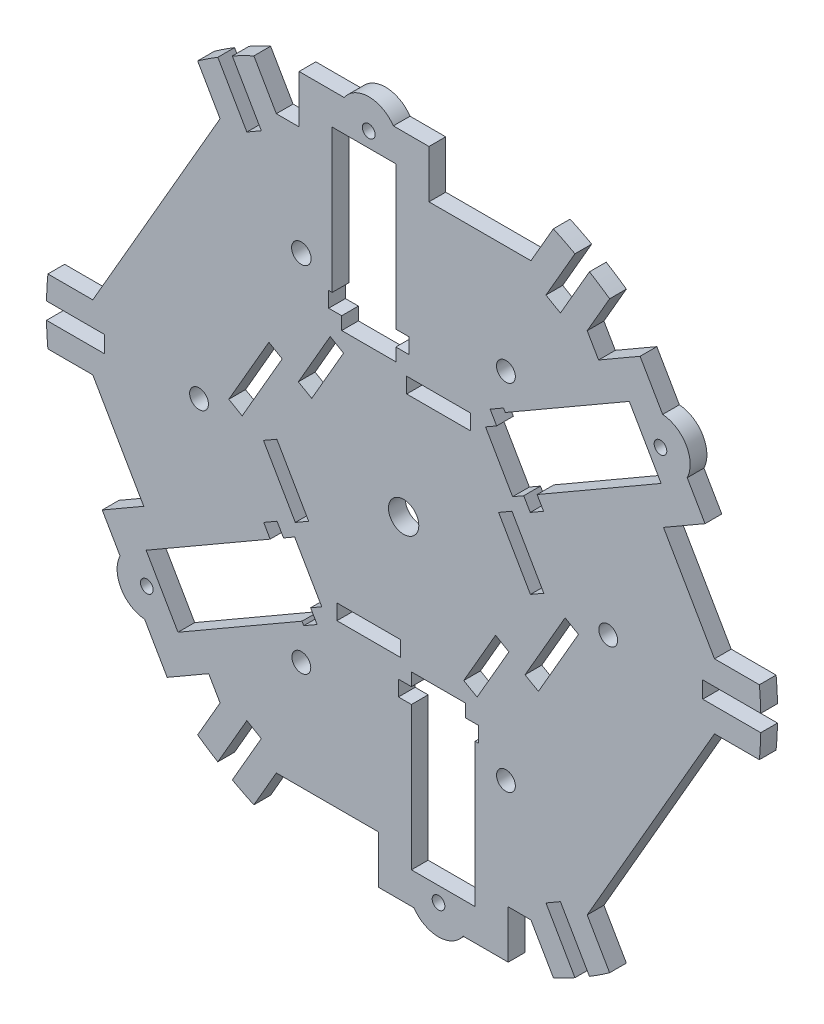
SolidWorks part; units mm, degrees
ref_plane "Front Plane" through (0, 0, 0) normal (0, 0, 1) x (1, 0, 0)
ref_plane "Top Plane" through (0, 0, 0) normal (0, 1, 0) x (1, 0, 0)
ref_plane "Right Plane" through (0, 0, 0) normal (1, 0, 0) x (0, 0, -1)
sketch "Model" plane through (0, 0, 0) normal (0, 0, 1) x (1, 0, 0)
  line L0 (33.3939, 18.31) -> (29.1071, 15.835) construction
  line L1 (43.2939, 1.1627) -> (33.3939, 18.31) construction
  line L2 (39.0071, -1.3123) -> (43.2939, 1.1627) construction
  line L3 (29.1071, 15.835) -> (39.0071, -1.3123) construction
  line L4 (32.5539, -19.765) -> (28.2671, -17.29) construction
  line L5 (22.6539, -36.9123) -> (32.5539, -19.765) construction
  line L6 (18.3671, -34.4373) -> (22.6539, -36.9123) construction
  line L7 (28.2671, -17.29) -> (18.3671, -34.4373) construction
  line L8 (-0.84, -38.075) -> (-0.84, -33.125) construction
  line L9 (-20.64, -38.075) -> (-0.84, -38.075) construction
  line L10 (-20.64, -33.125) -> (-20.64, -38.075) construction
  line L11 (-0.84, -33.125) -> (-20.64, -33.125) construction
  line L12 (-33.3939, -18.31) -> (-29.1071, -15.835) construction
  line L13 (-43.2939, -1.1627) -> (-33.3939, -18.31) construction
  line L14 (-39.0071, 1.3123) -> (-43.2939, -1.1627) construction
  line L15 (-29.1071, -15.835) -> (-39.0071, 1.3123) construction
  line L16 (-32.5539, 19.765) -> (-28.2671, 17.29) construction
  line L17 (-22.6539, 36.9123) -> (-32.5539, 19.765) construction
  line L18 (-18.3671, 34.4373) -> (-22.6539, 36.9123) construction
  line L19 (-28.2671, 17.29) -> (-18.3671, 34.4373) construction
  line L20 (36.9463, 23.9861) -> (38.946, 20.5225) construction
  line L21 (33.5255, 22.0111) -> (36.9463, 23.9861) construction
  line L22 (25.0855, 36.6296) -> (33.5255, 22.0111) construction
  line L23 (28.5063, 38.6046) -> (25.0855, 36.6296) construction
  line L24 (26.506, 42.0692) -> (28.5063, 38.6046) construction
  line L25 (30.7928, 44.5442) -> (26.506, 42.0692) construction
  line L26 (30.7928, 44.5442) -> (31.3331, 43.6084) construction
  line L27 (33.3573, 18.1734) -> (29.2437, 15.7984)
  line L28 (69.5248, 65.6584) -> (31.3331, 43.6084) construction
  line L29 (79.4248, 48.5111) -> (69.5248, 65.6584) construction
  line L30 (41.2331, 26.4611) -> (79.4248, 48.5111) construction
  line L31 (43.2328, 22.9975) -> (41.2331, 26.4611) construction
  line L32 (38.946, 20.5225) -> (43.2328, 22.9975) construction
  line L33 (37.246, -23.467) -> (41.5328, -25.942) construction
  line L34 (49.686, -1.9203) -> (37.246, -23.467) construction
  line L35 (53.9728, -4.3953) -> (49.686, -1.9203) construction
  line L36 (41.5328, -25.942) -> (53.9728, -4.3953) construction
  line L37 (2.3, -43.9895) -> (-1.7, -43.9895) construction
  line L38 (2.3, -40.0395) -> (2.3, -43.9895) construction
  line L39 (19.18, -40.0395) -> (2.3, -40.0395) construction
  line L40 (19.18, -43.9895) -> (19.18, -40.0395) construction
  line L41 (23.18, -43.9895) -> (19.18, -43.9895) construction
  line L42 (23.18, -48.9395) -> (23.18, -43.9895) construction
  line L43 (22.1, -48.9395) -> (23.18, -48.9395) construction
  line L44 (22.1, -93.0395) -> (22.1, -48.9395) construction
  line L45 (2.3, -93.0395) -> (22.1, -93.0395) construction
  line L46 (2.3, -48.9395) -> (2.3, -93.0395) construction
  line L47 (-1.7, -48.9395) -> (2.3, -48.9395) construction
  line L48 (-1.7, -43.9895) -> (-1.7, -48.9395) construction
  line L49 (-36.9457, -23.9871) -> (-38.946, -20.5225) construction
  line L50 (-33.5249, -22.0121) -> (-36.9457, -23.9871) construction
  line L51 (-25.0849, -36.6306) -> (-33.5249, -22.0121) construction
  line L52 (-28.5057, -38.6056) -> (-25.0849, -36.6306) construction
  line L53 (-26.506, -42.0692) -> (-28.5057, -38.6056) construction
  line L54 (-30.7928, -44.5442) -> (-26.506, -42.0692) construction
  line L55 (-31.3325, -43.6094) -> (-30.7928, -44.5442) construction
  line L56 (-69.5242, -65.6594) -> (-31.3325, -43.6094) construction
  line L57 (-79.4242, -48.5121) -> (-69.5242, -65.6594) construction
  line L58 (-41.2325, -26.4621) -> (-79.4242, -48.5121) construction
  line L59 (-43.2328, -22.9975) -> (-41.2325, -26.4621) construction
  line L60 (-38.946, -20.5225) -> (-43.2328, -22.9975) construction
  line L61 (-37.246, 23.467) -> (-41.5328, 25.942) construction
  line L62 (-49.686, 1.9203) -> (-37.246, 23.467) construction
  line L63 (-53.9728, 4.3953) -> (-49.686, 1.9203) construction
  line L64 (-41.5328, 25.942) -> (-53.9728, 4.3953) construction
  line L65 (0.84, 38.075) -> (0.84, 33.125) construction
  line L66 (20.64, 38.075) -> (0.84, 38.075) construction
  line L67 (20.64, 33.125) -> (20.64, 38.075) construction
  line L68 (0.84, 33.125) -> (20.64, 33.125) construction
  line L69 (-2.3, 43.9895) -> (1.7, 43.9895) construction
  line L70 (-2.3, 40.0395) -> (-2.3, 43.9895) construction
  line L71 (-19.18, 40.0395) -> (-2.3, 40.0395) construction
  line L72 (-19.18, 43.9895) -> (-19.18, 40.0395) construction
  line L73 (-23.18, 43.9895) -> (-19.18, 43.9895) construction
  line L74 (-23.18, 48.9395) -> (-23.18, 43.9895) construction
  line L75 (-22.1, 48.9395) -> (-23.18, 48.9395) construction
  line L76 (-22.1, 93.0395) -> (-22.1, 48.9395) construction
  line L77 (-2.3, 93.0395) -> (-22.1, 93.0395) construction
  line L78 (-2.3, 48.9395) -> (-2.3, 93.0395) construction
  line L79 (1.7, 48.9395) -> (-2.3, 48.9395) construction
  line L80 (1.7, 43.9895) -> (1.7, 48.9395) construction
  line L81 (43.9566, 81.085) -> (48.2434, 78.61) construction
  line L82 (52.8927, 96.5628) -> (43.9566, 81.085) construction
  line L83 (46.071, 99.9974) -> (39.1423, 87.9964) construction
  line L84 (39.1423, 87.9964) -> (7.9, 87.9964) construction
  line L85 (7.9, 87.9964) -> (7.9, 102.7645) construction
  line L86 (7.9, 102.7645) -> (-3.1242, 102.7645) construction
  line L87 (-18.3558, 102.7645) -> (-32.3, 102.7645) construction
  line L88 (-32.3, 102.7645) -> (-32.3, 87.9964) construction
  line L89 (-32.3, 87.9964) -> (-39.1423, 87.9964) construction
  line L90 (-39.1423, 87.9964) -> (-46.071, 99.9974) construction
  line L91 (-43.9566, 81.085) -> (-52.8927, 96.5628) construction
  line L92 (-48.2434, 78.61) -> (-43.9566, 81.085) construction
  line L93 (-57.1795, 94.0878) -> (-48.2434, 78.61) construction
  line L94 (-63.565, 89.8972) -> (-56.6362, 77.8962) construction
  line L95 (-56.6362, 77.8962) -> (-95.7785, 10.0998) construction
  line L96 (-95.7785, 10.0998) -> (-109.6358, 10.0998) construction
  line L97 (-92.2, 2.475) -> (-110.0722, 2.475) construction
  line L98 (-92.2, -2.475) -> (-92.2, 2.475) construction
  line L99 (-110.0722, -2.475) -> (-92.2, -2.475) construction
  line L100 (-109.6357, -10.1005) -> (-95.7779, -10.1005) construction
  line L101 (-95.7779, -10.1005) -> (-80.1568, -37.1571) construction
  line L102 (-80.1568, -37.1571) -> (-92.9463, -44.5411) construction
  line L103 (-92.9463, -44.5411) -> (-87.4342, -54.0884) construction
  line L104 (-79.8184, -67.2793) -> (-72.8463, -79.3553) construction
  line L105 (-72.8463, -79.3553) -> (-60.0568, -71.9713) construction
  line L106 (-60.0568, -71.9713) -> (-56.6357, -77.8969) construction
  line L107 (-56.6357, -77.8969) -> (-63.5643, -89.8976) construction
  line L108 (-48.2434, -78.61) -> (-57.1795, -94.0878) construction
  line L109 (-43.9566, -81.085) -> (-48.2434, -78.61) construction
  line L110 (-52.8927, -96.5628) -> (-43.9566, -81.085) construction
  line L111 (-46.071, -99.9974) -> (-39.1423, -87.9964) construction
  line L112 (-39.1423, -87.9964) -> (-7.9, -87.9964) construction
  line L113 (-7.9, -87.9964) -> (-7.9, -102.7645) construction
  line L114 (-7.9, -102.7645) -> (3.1242, -102.7645) construction
  line L115 (18.3558, -102.7645) -> (32.3, -102.7645) construction
  line L116 (32.3, -102.7645) -> (32.3, -87.9964) construction
  line L117 (32.3, -87.9964) -> (39.1423, -87.9964) construction
  line L118 (39.1423, -87.9964) -> (46.071, -99.9974) construction
  line L119 (43.9566, -81.085) -> (52.8927, -96.5628) construction
  line L120 (48.2434, -78.61) -> (43.9566, -81.085) construction
  line L121 (57.1795, -94.0878) -> (48.2434, -78.61) construction
  line L122 (63.5645, -89.8975) -> (56.6358, -77.8966) construction
  line L123 (56.6358, -77.8966) -> (95.778, -10.1002) construction
  line L124 (95.778, -10.1002) -> (109.6357, -10.1002) construction
  line L125 (92.2, -2.475) -> (110.0722, -2.475) construction
  line L126 (92.2, 2.475) -> (92.2, -2.475) construction
  line L127 (110.0722, 2.475) -> (92.2, 2.475) construction
  line L128 (109.6358, 10.0995) -> (95.7786, 10.0995) construction
  line L129 (95.7786, 10.0995) -> (80.1574, 37.1561) construction
  line L130 (80.1574, 37.1561) -> (92.9469, 44.5402) construction
  line L131 (92.9469, 44.5402) -> (87.4348, 54.0874) construction
  line L132 (79.8191, 67.2783) -> (72.8469, 79.3544) construction
  line L133 (72.8469, 79.3544) -> (60.0574, 71.9703) construction
  line L134 (60.0574, 71.9703) -> (56.6363, 77.8959) construction
  line L135 (56.6363, 77.8959) -> (63.5652, 89.8971) construction
  line L136 (48.2434, 78.61) -> (57.1795, 94.0878) construction
  line L137 (29.2437, 15.7984) -> (39.0437, -1.1757)
  line L138 (39.0437, -1.1757) -> (43.1573, 1.1993)
  line L139 (43.1573, 1.1993) -> (33.3573, 18.1734)
  line L140 (32.4173, -19.8016) -> (28.3037, -17.4266)
  line L141 (28.3037, -17.4266) -> (18.5037, -34.4007)
  line L142 (18.5037, -34.4007) -> (22.6173, -36.7757)
  line L143 (22.6173, -36.7757) -> (32.4173, -19.8016)
  line L144 (-0.94, -37.975) -> (-0.94, -33.225)
  line L145 (-0.94, -33.225) -> (-20.54, -33.225)
  line L146 (-20.54, -33.225) -> (-20.54, -37.975)
  line L147 (-20.54, -37.975) -> (-0.94, -37.975)
  line L148 (-33.3573, -18.1734) -> (-29.2437, -15.7984)
  line L149 (-29.2437, -15.7984) -> (-39.0437, 1.1757)
  line L150 (-39.0437, 1.1757) -> (-43.1573, -1.1993)
  line L151 (-43.1573, -1.1993) -> (-33.3573, -18.1734)
  line L152 (-32.4173, 19.8016) -> (-28.3037, 17.4266)
  line L153 (-28.3037, 17.4266) -> (-18.5037, 34.4007)
  line L154 (-18.5037, 34.4007) -> (-22.6173, 36.7757)
  line L155 (-22.6173, 36.7757) -> (-32.4173, 19.8016)
  line L156 (36.9829, 24.1227) -> (38.9826, 20.6591)
  line L157 (38.9826, 20.6591) -> (43.0962, 23.0341)
  line L158 (43.0962, 23.0341) -> (41.0965, 26.4977)
  line L159 (41.0965, 26.4977) -> (79.2882, 48.5477)
  line L160 (79.2882, 48.5477) -> (69.4882, 65.5218)
  line L161 (69.4882, 65.5218) -> (31.2965, 43.4718)
  line L162 (30.7562, 44.4076) -> (31.2965, 43.4718)
  line L163 (30.7562, 44.4076) -> (26.6426, 42.0326)
  line L164 (26.6426, 42.0326) -> (28.6429, 38.568)
  line L165 (28.6429, 38.568) -> (25.2221, 36.593)
  line L166 (25.2221, 36.593) -> (33.5621, 22.1477)
  line L167 (33.5621, 22.1477) -> (36.9829, 24.1227)
  line L168 (37.3826, -23.4304) -> (41.4962, -25.8054)
  line L169 (41.4962, -25.8054) -> (53.8362, -4.4319)
  line L170 (53.8362, -4.4319) -> (49.7226, -2.0569)
  line L171 (49.7226, -2.0569) -> (37.3826, -23.4304)
  line L172 (2.4, -44.0895) -> (-1.6, -44.0895)
  line L173 (-1.6, -44.0895) -> (-1.6, -48.8395)
  line L174 (-1.6, -48.8395) -> (2.4, -48.8395)
  line L175 (2.4, -48.8395) -> (2.4, -92.9395)
  line L176 (2.4, -92.9395) -> (22, -92.9395)
  line L177 (22, -92.9395) -> (22, -48.8395)
  line L178 (22, -48.8395) -> (23.08, -48.8395)
  line L179 (23.08, -48.8395) -> (23.08, -44.0895)
  line L180 (23.08, -44.0895) -> (19.08, -44.0895)
  line L181 (19.08, -44.0895) -> (19.08, -40.1395)
  line L182 (19.08, -40.1395) -> (2.4, -40.1395)
  line L183 (2.4, -40.1395) -> (2.4, -44.0895)
  line L184 (-36.9823, -24.1237) -> (-38.9826, -20.6591)
  line L185 (-38.9826, -20.6591) -> (-43.0962, -23.0341)
  line L186 (-43.0962, -23.0341) -> (-41.0959, -26.4987)
  line L187 (-41.0959, -26.4987) -> (-79.2876, -48.5487)
  line L188 (-79.2876, -48.5487) -> (-69.4876, -65.5228)
  line L189 (-69.4876, -65.5228) -> (-31.2959, -43.4728)
  line L190 (-31.2959, -43.4728) -> (-30.7562, -44.4076)
  line L191 (-30.7562, -44.4076) -> (-26.6426, -42.0326)
  line L192 (-26.6426, -42.0326) -> (-28.6423, -38.569)
  line L193 (-28.6423, -38.569) -> (-25.2215, -36.594)
  line L194 (-25.2215, -36.594) -> (-33.5615, -22.1487)
  line L195 (-33.5615, -22.1487) -> (-36.9823, -24.1237)
  line L196 (-37.3826, 23.4304) -> (-41.4962, 25.8054)
  line L197 (-41.4962, 25.8054) -> (-53.8362, 4.4319)
  line L198 (-53.8362, 4.4319) -> (-49.7226, 2.0569)
  line L199 (-49.7226, 2.0569) -> (-37.3826, 23.4304)
  line L200 (0.94, 37.975) -> (0.94, 33.225)
  line L201 (0.94, 33.225) -> (20.54, 33.225)
  line L202 (20.54, 33.225) -> (20.54, 37.975)
  line L203 (20.54, 37.975) -> (0.94, 37.975)
  line L204 (-2.4, 44.0895) -> (1.6, 44.0895)
  line L205 (1.6, 44.0895) -> (1.6, 48.8395)
  line L206 (1.6, 48.8395) -> (-2.4, 48.8395)
  line L207 (-2.4, 48.8395) -> (-2.4, 92.9395)
  line L208 (-2.4, 92.9395) -> (-22, 92.9395)
  line L209 (-22, 92.9395) -> (-22, 48.8395)
  line L210 (-22, 48.8395) -> (-23.08, 48.8395)
  line L211 (-23.08, 48.8395) -> (-23.08, 44.0895)
  line L212 (-23.08, 44.0895) -> (-19.08, 44.0895)
  line L213 (-19.08, 44.0895) -> (-19.08, 40.1395)
  line L214 (-19.08, 40.1395) -> (-2.4, 40.1395)
  line L215 (-2.4, 40.1395) -> (-2.4, 44.0895)
  line L216 (43.82, 81.0484) -> (48.28, 78.4734)
  line L217 (48.28, 78.4734) -> (57.2149, 93.9492)
  line L218 (56.5208, 77.8959) -> (63.4329, 89.868)
  line L219 (60.0208, 71.8337) -> (56.5208, 77.8959)
  line L220 (72.8103, 79.2178) -> (60.0208, 71.8337)
  line L221 (79.7588, 67.1827) -> (72.8103, 79.2178)
  line L222 (92.8103, 44.5768) -> (87.3219, 54.0831)
  line L223 (80.0208, 37.1927) -> (92.8103, 44.5768)
  line L224 (95.7208, 9.9995) -> (80.0208, 37.1927)
  line L225 (109.5446, 9.9995) -> (95.7208, 9.9995)
  line L226 (109.9699, 2.575) -> (92.1, 2.575)
  line L227 (92.1, 2.575) -> (92.1, -2.575)
  line L228 (92.1, -2.575) -> (109.9699, -2.575)
  line L229 (95.7203, -10.0002) -> (109.5445, -10.0002)
  line L230 (56.5203, -77.8966) -> (95.7203, -10.0002)
  line L231 (63.4323, -89.8685) -> (56.5203, -77.8966)
  line L232 (57.2149, -93.9492) -> (48.28, -78.4734)
  line L233 (48.28, -78.4734) -> (43.82, -81.0484)
  line L234 (43.82, -81.0484) -> (52.7549, -96.5242)
  line L235 (39.2, -87.8964) -> (46.112, -99.8683)
  line L236 (32.2, -87.8964) -> (39.2, -87.8964)
  line L237 (32.2, -102.6645) -> (32.2, -87.8964)
  line L238 (18.3031, -102.6645) -> (32.2, -102.6645)
  line L239 (-7.8, -102.6645) -> (3.1769, -102.6645)
  line L240 (-7.8, -87.8964) -> (-7.8, -102.6645)
  line L241 (-39.2, -87.8964) -> (-7.8, -87.8964)
  line L242 (-46.112, -99.8683) -> (-39.2, -87.8964)
  line L243 (-52.7549, -96.5242) -> (-43.82, -81.0484)
  line L244 (-43.82, -81.0484) -> (-48.28, -78.4734)
  line L245 (-48.28, -78.4734) -> (-57.2149, -93.9492)
  line L246 (-56.5202, -77.8969) -> (-63.4321, -89.8686)
  line L247 (-60.0202, -71.8347) -> (-56.5202, -77.8969)
  line L248 (-72.8097, -79.2187) -> (-60.0202, -71.8347)
  line L249 (-79.7582, -67.1836) -> (-72.8097, -79.2187)
  line L250 (-92.8097, -44.5777) -> (-87.3212, -54.084)
  line L251 (-80.0202, -37.1937) -> (-92.8097, -44.5777)
  line L252 (-95.7202, -10.0005) -> (-80.0202, -37.1937)
  line L253 (-109.5445, -10.0005) -> (-95.7202, -10.0005)
  line L254 (-109.9699, -2.575) -> (-92.1, -2.575)
  line L255 (-92.1, -2.575) -> (-92.1, 2.575)
  line L256 (-92.1, 2.575) -> (-109.9699, 2.575)
  line L257 (-95.7207, 9.9998) -> (-109.5445, 9.9998)
  line L258 (-56.5207, 77.8962) -> (-95.7207, 9.9998)
  line L259 (-63.4327, 89.8682) -> (-56.5207, 77.8962)
  line L260 (-57.2149, 93.9492) -> (-48.28, 78.4734)
  line L261 (-48.28, 78.4734) -> (-43.82, 81.0484)
  line L262 (-43.82, 81.0484) -> (-52.7549, 96.5242)
  line L263 (-39.2, 87.8964) -> (-46.112, 99.8683)
  line L264 (-32.2, 87.8964) -> (-39.2, 87.8964)
  line L265 (-32.2, 102.6645) -> (-32.2, 87.8964)
  line L266 (-18.3031, 102.6645) -> (-32.2, 102.6645)
  line L267 (7.8, 102.6645) -> (-3.1769, 102.6645)
  line L268 (7.8, 87.8964) -> (7.8, 102.6645)
  line L269 (39.2, 87.8964) -> (7.8, 87.8964)
  line L270 (46.112, 99.8683) -> (39.2, 87.8964)
  line L271 (52.7549, 96.5242) -> (43.82, 81.0484)
  circle A0 centre (-63, 0) radius 3 construction
  circle A1 centre (-31.5, -54.5596) radius 3 construction
  circle A2 centre (31.5, -54.5596) radius 3 construction
  circle A3 centre (63, 0) radius 3 construction
  circle A4 centre (31.5, 54.5596) radius 3 construction
  circle A5 centre (-31.5, 54.5596) radius 3.1 construction
  circle A6 centre (-79.0797, -58.0588) radius 2.05 construction
  circle A7 centre (79.0803, 58.0579) radius 2.05 construction
  circle A8 centre (0, 0) radius 4.765 construction
  circle A9 centre (-10.74, 97.5145) radius 2.05 construction
  circle A10 centre (10.74, -97.5145) radius 2.05 construction
  arc A11 (52.8927, 96.5628) -> (46.071, 99.9974) centre (0, 0) ccw construction
  arc A12 (-3.1242, 102.7645) -> (-18.3558, 102.7645) centre (-10.74, 97.5145) ccw construction
  arc A13 (-46.071, 99.9974) -> (-52.8927, 96.5628) centre (0, 0) ccw construction
  arc A14 (-57.1795, 94.0878) -> (-63.565, 89.8972) centre (0, 0) ccw construction
  arc A15 (-109.6358, 10.0998) -> (-110.0722, 2.475) centre (0, 0) ccw construction
  arc A16 (-110.0722, -2.475) -> (-109.6357, -10.1005) centre (0, 0) ccw construction
  arc A17 (-87.4342, -54.0884) -> (-79.8184, -67.2793) centre (-79.0797, -58.0588) ccw construction
  arc A18 (-63.5643, -89.8976) -> (-57.1795, -94.0878) centre (0, 0) ccw construction
  arc A19 (-52.8927, -96.5628) -> (-46.071, -99.9974) centre (0, 0) ccw construction
  arc A20 (3.1242, -102.7645) -> (18.3558, -102.7645) centre (10.74, -97.5145) ccw construction
  arc A21 (46.071, -99.9974) -> (52.8927, -96.5628) centre (0, 0) ccw construction
  arc A22 (57.1795, -94.0878) -> (63.5645, -89.8975) centre (0, 0) ccw construction
  arc A23 (109.6357, -10.1002) -> (110.0722, -2.475) centre (0, 0) ccw construction
  arc A24 (110.0722, 2.475) -> (109.6358, 10.0995) centre (0, 0) ccw construction
  arc A25 (87.4348, 54.0874) -> (79.8191, 67.2783) centre (79.0803, 58.0579) ccw construction
  arc A26 (63.5652, 89.8971) -> (57.1795, 94.0878) centre (0, 0) ccw construction
  arc A27 (63.4329, 89.868) -> (57.2149, 93.9492) centre (0, 0) ccw
  arc A28 (87.3219, 54.0831) -> (79.7588, 67.1827) centre (79.0803, 58.0579) ccw
  arc A29 (109.9699, 2.575) -> (109.5446, 9.9995) centre (0, 0) ccw
  arc A30 (109.5445, -10.0002) -> (109.9699, -2.575) centre (0, 0) ccw
  arc A31 (57.2149, -93.9492) -> (63.4323, -89.8685) centre (0, 0) ccw
  arc A32 (46.112, -99.8683) -> (52.7549, -96.5242) centre (0, 0) ccw
  arc A33 (3.1769, -102.6645) -> (18.3031, -102.6645) centre (10.74, -97.5145) ccw
  arc A34 (-52.7549, -96.5242) -> (-46.112, -99.8683) centre (0, 0) ccw
  arc A35 (-63.4321, -89.8686) -> (-57.2149, -93.9492) centre (0, 0) ccw
  arc A36 (-87.3212, -54.084) -> (-79.7582, -67.1836) centre (-79.0797, -58.0588) ccw
  arc A37 (-109.9699, -2.575) -> (-109.5445, -10.0005) centre (0, 0) ccw
  arc A38 (-109.5445, 9.9998) -> (-109.9699, 2.575) centre (0, 0) ccw
  arc A39 (-57.2149, 93.9492) -> (-63.4327, 89.8682) centre (0, 0) ccw
  arc A40 (-46.112, 99.8683) -> (-52.7549, 96.5242) centre (0, 0) ccw
  arc A41 (-3.1769, 102.6645) -> (-18.3031, 102.6645) centre (-10.74, 97.5145) ccw
  arc A42 (52.7549, 96.5242) -> (46.112, 99.8683) centre (0, 0) ccw
  circle A43 centre (-63, 0) radius 2.9
  circle A44 centre (-31.5, -54.5596) radius 2.9
  circle A45 centre (31.5, -54.5596) radius 2.9
  circle A46 centre (63, 0) radius 2.9
  circle A47 centre (31.5, 54.5596) radius 2.9
  circle A48 centre (-31.5, 54.5596) radius 3
  circle A49 centre (-79.0797, -58.0588) radius 1.95
  circle A50 centre (79.0803, 58.0579) radius 1.95
  circle A51 centre (0, 0) radius 4.665
  circle A52 centre (-10.74, 97.5145) radius 1.95
  circle A53 centre (10.74, -97.5145) radius 1.95
  dimension "D1" = 0.1
extrude "Boss-Extrude1" add sketch "Model" along normal blind 5.15
